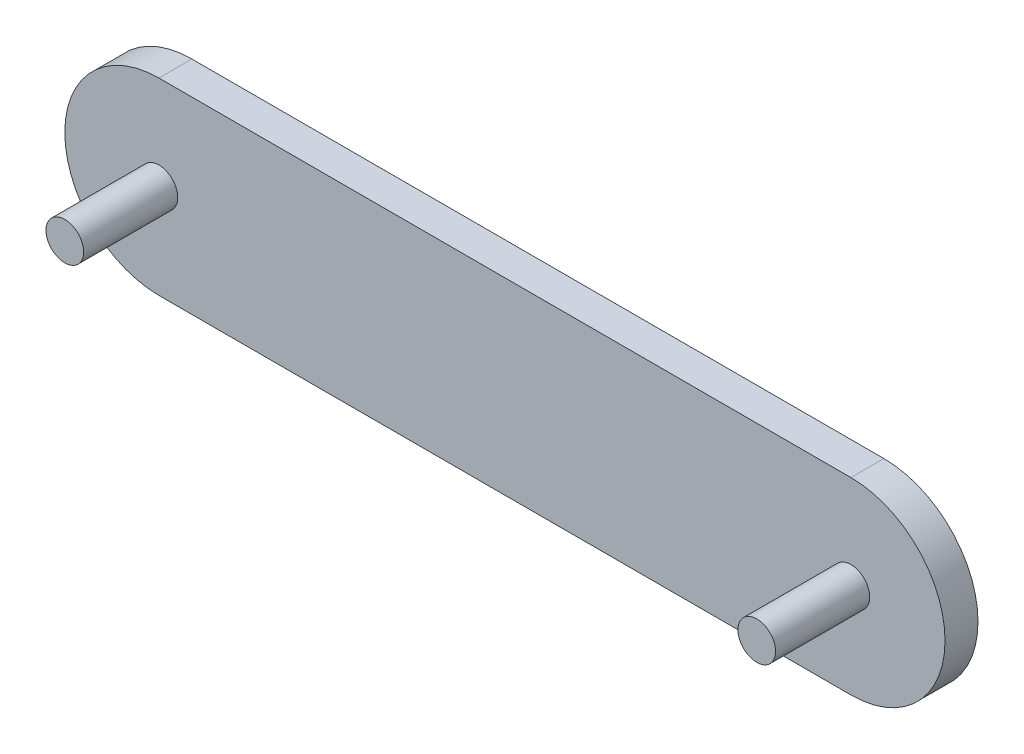
SolidWorks part; units mm, degrees
ref_plane "Front Plane" through (0, 0, 0) normal (0, 0, 1) x (1, 0, 0)
ref_plane "Top Plane" through (0, 0, 0) normal (0, 1, 0) x (1, 0, 0)
ref_plane "Right Plane" through (0, 0, 0) normal (1, 0, 0) x (0, 0, -1)
sketch "Sketch2" plane through (0, 0, 0) normal (0, 0, 1) x (1, 0, 0)
  line L0 (0, 0) -> (147, 0)
  line L3 (0, 40) -> (147, 40)
  arc A0 (0, 40) -> (0, 0) centre (0, 20) ccw
  arc A2 (147, 0) -> (147, 40) centre (147, 20) ccw
  dimension "D2" = 20
  dimension "D3" = 20
  dimension "D1" = 147
extrude "Boss-Extrude1" add sketch "Sketch2" along normal blind 7
sketch "Sketch3" plane through (0, 0, 7) normal (0, 0, 1) x (1, 0, 0)
  line L0 (147, 40) -> (0, 40) construction
  circle A1 centre (147, 20) radius 4
  dimension "D1" = 8
  dimension "D2" = 20
extrude "Boss-Extrude2" add sketch "Sketch3" along normal blind 20
sketch "Sketch4" plane through (0, 0, 7) normal (0, 0, 1) x (1, 0, 0)
  circle A0 centre (0, 20) radius 4
  dimension "D1" = 8
extrude "Boss-Extrude3" add sketch "Sketch4" along normal blind 20
